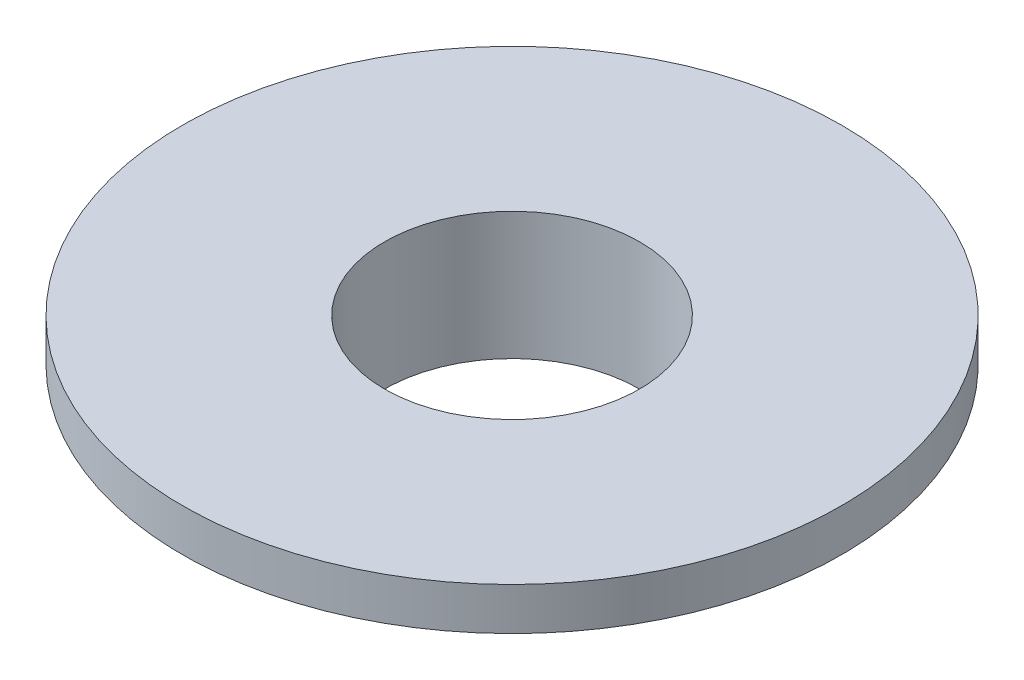
SolidWorks part; units mm, degrees
material "Сталь ШХ15 ГОСТ 801-78"
ref_plane "Plane1" through (0, 0, 0) normal (0, 0, 1) x (1, 0, 0)
ref_plane "Plane2" through (0, 0, 0) normal (0, 1, 0) x (1, 0, 0)
ref_plane "Plane3" through (0, 0, 0) normal (1, 0, 0) x (0, 0, -1)
sketch "Эскиз1" plane through (0, 0, 0) normal (0, 0, 1) x (1, 0, 0)
  line L6 (0, 0) -> (0, 6.4893) construction
  line L7 (6, 0) -> (6, 6)
  line L8 (6, 6) -> (15.5, 6)
  line L9 (15.5, 6) -> (15.5, 4)
  line L10 (15.5, 4) -> (6.7, 4)
  line L11 (6.7, 4) -> (6.7, 0)
  line L12 (6.7, 0) -> (6, 0)
  dimension "D1" = 6
  dimension "D2" = 6.7
  dimension "D3" = 15.5
  dimension "D4" = 2
  dimension "D5" = 6
  dimension "D6" = 0
revolve "Повернуть1" add sketch "Эскиз1" angle 360 about L6
